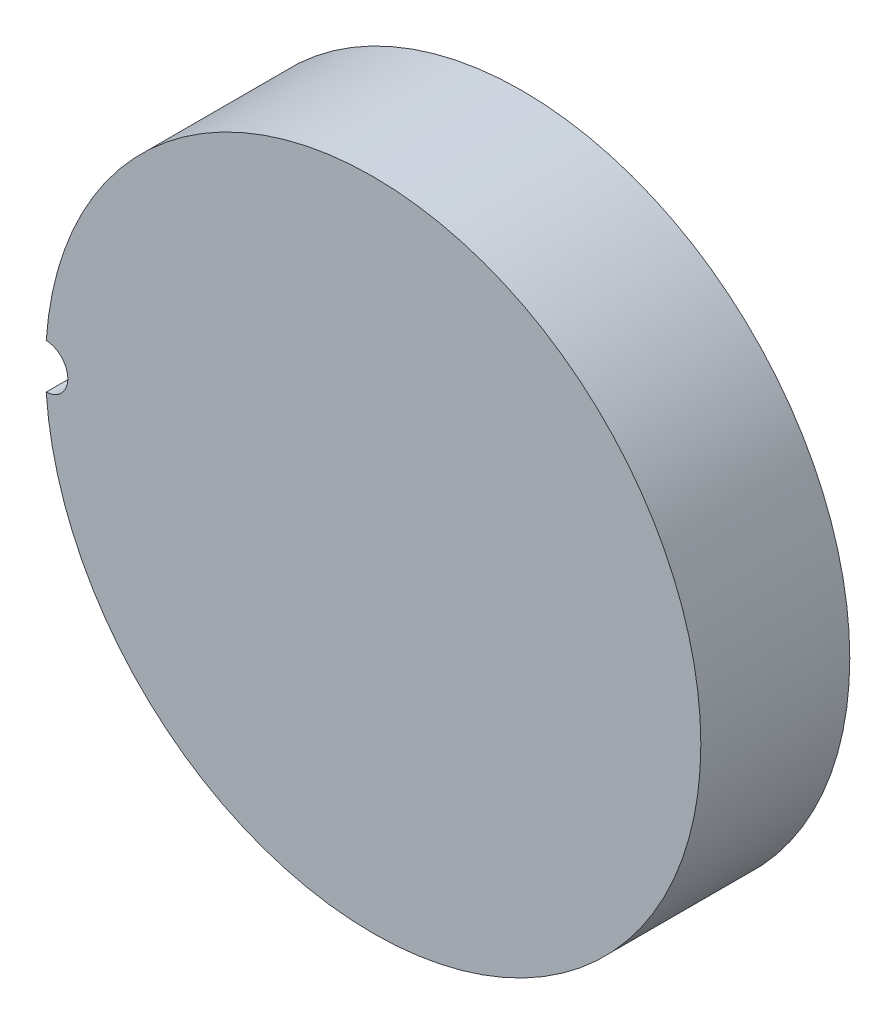
SolidWorks part; units mm, degrees
ref_plane "Front Plane" through (0, 0, 0) normal (0, 0, 1) x (1, 0, 0)
ref_plane "Top Plane" through (0, 0, 0) normal (0, 1, 0) x (1, 0, 0)
ref_plane "Right Plane" through (0, 0, 0) normal (1, 0, 0) x (0, 0, -1)
sketch "Sketch1" plane through (0, 0, 0) normal (0, 1, 0) x (1, 0, 0)
  line L0 (0, 15.8949) -> (0, 0)
  line L1 (0, 0) -> (22, 0)
  line L2 (22, 0) -> (22, 10)
  line L3 (0, -18.6718) -> (0, 10.7732) construction
  arc A0 (0, 15.8949) -> (22, 10) centre (0, -28.1051) cw
  dimension "D4" = 44
  dimension "D1" = 22
  dimension "D3" = 10
revolve "Revolve1" add sketch "Sketch1" angle 360 about L3
sketch "Sketch2" plane through (0, 0, 0) normal (0, 0, 1) x (1, 0, 0)
  circle A0 centre (-22, 0) radius 1.5
  dimension "D2" = 22
  dimension "D1" = 3
extrude "Cut-Extrude1" cut sketch "Sketch2" against normal blind 5
